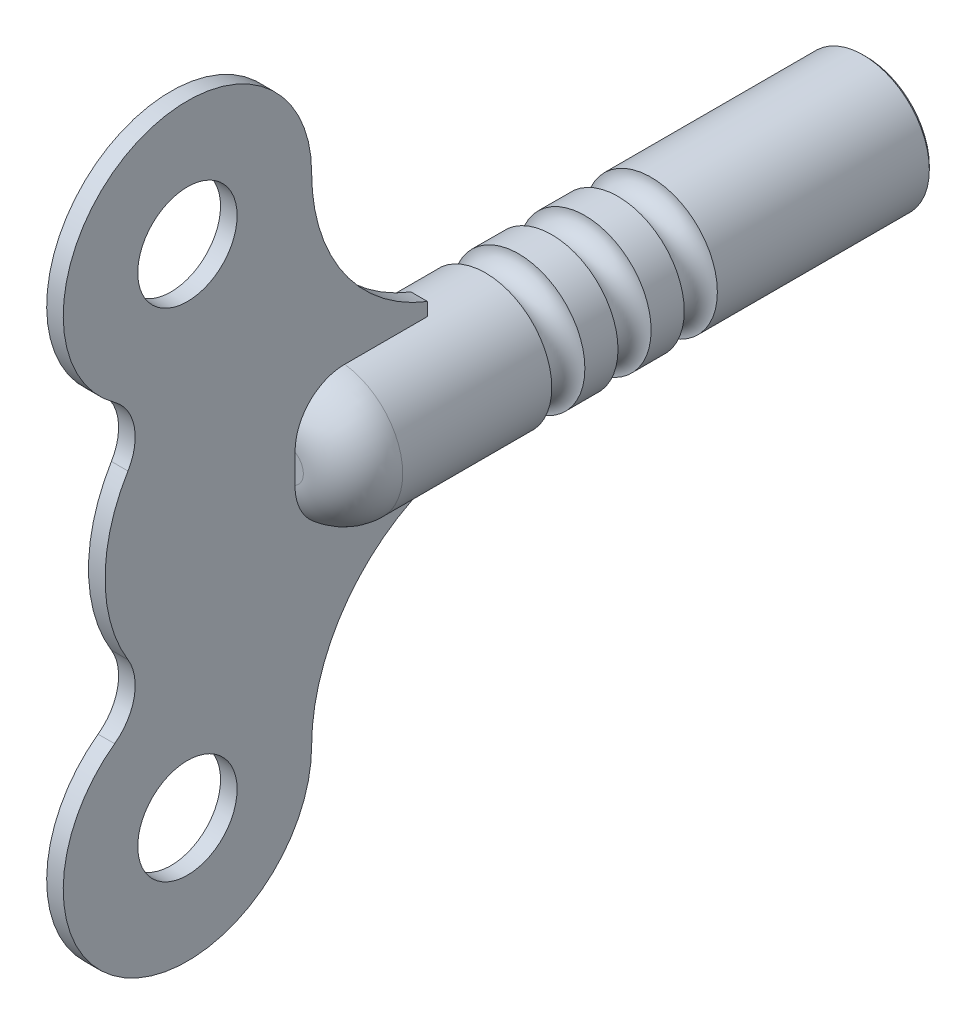
SolidWorks part; units mm, degrees
ref_plane "Front Plane" through (0, 0, 0) normal (0, 0, 1) x (1, 0, 0)
ref_plane "Top Plane" through (0, 0, 0) normal (0, 1, 0) x (1, 0, 0)
ref_plane "Right Plane" through (0, 0, 0) normal (1, 0, 0) x (0, 0, -1)
sketch "Sketch1" plane through (0, 0, 0) normal (0, 0, 1) x (1, 0, 0)
  circle A0 centre (0, -108.5) radius 4 construction
  circle A1 centre (0, -108.5) radius 4
extrude "Boss-Extrude1" add sketch "Sketch1" along normal blind 35
fillet "Fillet1" radius 3 1 edges at (4, -108.5, 35)
sketch "Sketch3" plane through (0, 0, 0) normal (1, 0, 0) x (0, 0, -1)
  line L0 (0, -108.5) -> (-55.9233, -108.5) construction
  line L1 (0, -112.5) -> (0, -104.5) construction
  line L2 (-49, -108.5) -> (-49, -87.3946) construction
  line L3 (0, -104.5) -> (-32, -104.5) construction
  line L4 (-23, -104.5) -> (-9.7083, -104.5) construction
  line L5 (-46.4732, -108.5) -> (-27, -108.5)
  line L6 (-23, -108.5) -> (-23, -104.5) construction
  line L7 (-35, -107.5) -> (-35, -109.5) construction
  line L8 (-27, -108.5) -> (-23, -108.5) construction
  line L9 (-27, -108.5) -> (-27, -103.747)
  circle A0 centre (-41.5, -93.5) radius 3
  arc A1 (-34, -93.5) -> (-42.6816, -100.9063) centre (-41.5, -93.5) ccw
  arc A2 (-42.6816, -100.9063) -> (-46.4732, -108.5) centre (-36.9732, -108.5) ccw
  arc A3 (-34, -93.5) -> (-27, -103.747) centre (-23, -93.5) ccw
  arc A4 (-27, -103.747) -> (-23, -104.5) centre (-23, -93.5) ccw construction
  dimension "D1" = 6
  dimension "D2" = 15
  dimension "D3" = 19
  dimension "D5" = 15
  dimension "D4" = 14
  dimension "D6" = 4
extrude "Boss-Extrude2" add sketch "Sketch3" along normal mid plane 1
mirror "Mirror1" about plane through (0.5, -108.5, 46.4732) normal (0, 1, 0) of "Boss-Extrude2"
fillet "Fillet2" radius 3 2 edges at (0, -116.0937, 42.6816) (0, -100.9063, 42.6816)
sketch "Sketch5" plane through (0, 0, 0) normal (0, 0, 1) x (1, 0, 0)
  line L0 (-2.4, -106.1) -> (-2.4, -110.9) construction
  line L1 (-2.4, -106.1) -> (2.4, -106.1) construction
  line L2 (2.4, -106.1) -> (2.4, -110.9) construction
  line L3 (-2.4, -110.9) -> (2.4, -110.9) construction
  line L4 (-2.4, -106.1) -> (-2.4, -110.9)
  line L5 (-2.4, -106.1) -> (2.4, -106.1)
  line L6 (2.4, -106.1) -> (2.4, -110.9)
  line L7 (-2.4, -110.9) -> (2.4, -110.9)
extrude "Cut-Extrude1" cut sketch "Sketch5" along normal blind 12
sketch "Sketch6" plane through (0, 0, 0) normal (1, 0, 0) x (0, 0, -1)
  line L0 (0, -104.5) -> (-27, -104.5) construction
  line L1 (-14, -104.5) -> (-18, -104.5) construction
  line L2 (-18, -104.5) -> (-22, -104.5) construction
  line L3 (0, -112.5) -> (0, -104.5) construction
  circle A0 centre (-14, -104.5) radius 1
  circle A1 centre (-18, -104.5) radius 1
  circle A2 centre (-22, -104.5) radius 1
  dimension "D1" = 2
  dimension "D2" = 4
  dimension "D3" = 14
revolve "Cut-Revolve1" cut sketch "Sketch6" angle 360 about axis through (0, -108.5, 35) along (0, 0, -1)
chamfer "Chamfer1" distance 0.2 angle 45 5 edges at (2.4, -108.5, 0) (0, -110.9, 0) (-2.4, -108.5, 0) (0, -106.1, 0) (4, -108.5, 0)
